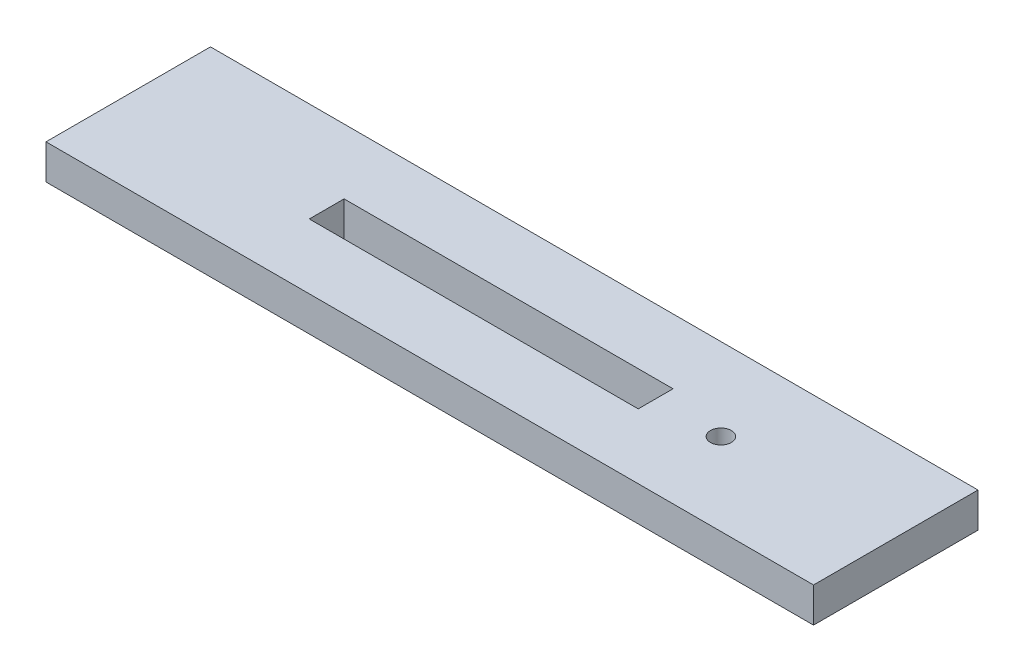
SolidWorks part; units mm, degrees
ref_plane "Front" through (0, 0, 0) normal (0, 0, 1) x (1, 0, 0)
ref_plane "Top" through (0, 0, 0) normal (0, 1, 0) x (1, 0, 0)
ref_plane "Right" through (0, 0, 0) normal (1, 0, 0) x (0, 0, -1)
sketch "Sketch1" plane through (0, 0, 0) normal (0, 1, 0) x (1, 0, 0)
  line L0 (-70, -2.4332) -> (70, -2.4332) construction
  line L1 (-70, -17.4332) -> (70, -17.4332)
  line L2 (-70, -17.4332) -> (-70, 12.5668)
  line L3 (-70, 12.5668) -> (70, 12.5668)
  line L4 (70, -17.4332) -> (70, 12.5668)
  line L6 (26.2, -5.6082) -> (-33.8, -5.6082)
  line L7 (26.2, -5.6082) -> (26.2, 0.7418)
  line L8 (26.2, 0.7418) -> (-33.8, 0.7418)
  line L9 (-33.8, -5.6082) -> (-33.8, 0.7418)
  line L10 (26.2, -5.6082) -> (-33.8, 0.7418) construction
  line L11 (26.2, 0.7418) -> (-33.8, -5.6082) construction
  circle A0 centre (38.1, -2.4332) radius 1.9
  point P0 (0, 0)
  point P6 (70, -2.4332)
  point P11 (-3.8, -2.4332)
  point P16 (26.2, -2.4332)
  dimension "D3" = 3.8
  dimension "D1" = 140
  dimension "D2" = 30
  dimension "D4" = 31.9
  dimension "D5" = 15
  dimension "D6" = 11.9
  dimension "D7" = 60
  dimension "D8" = 6.35
extrude "Boss-Extrude1" add sketch "Sketch1" along normal blind 6.35
